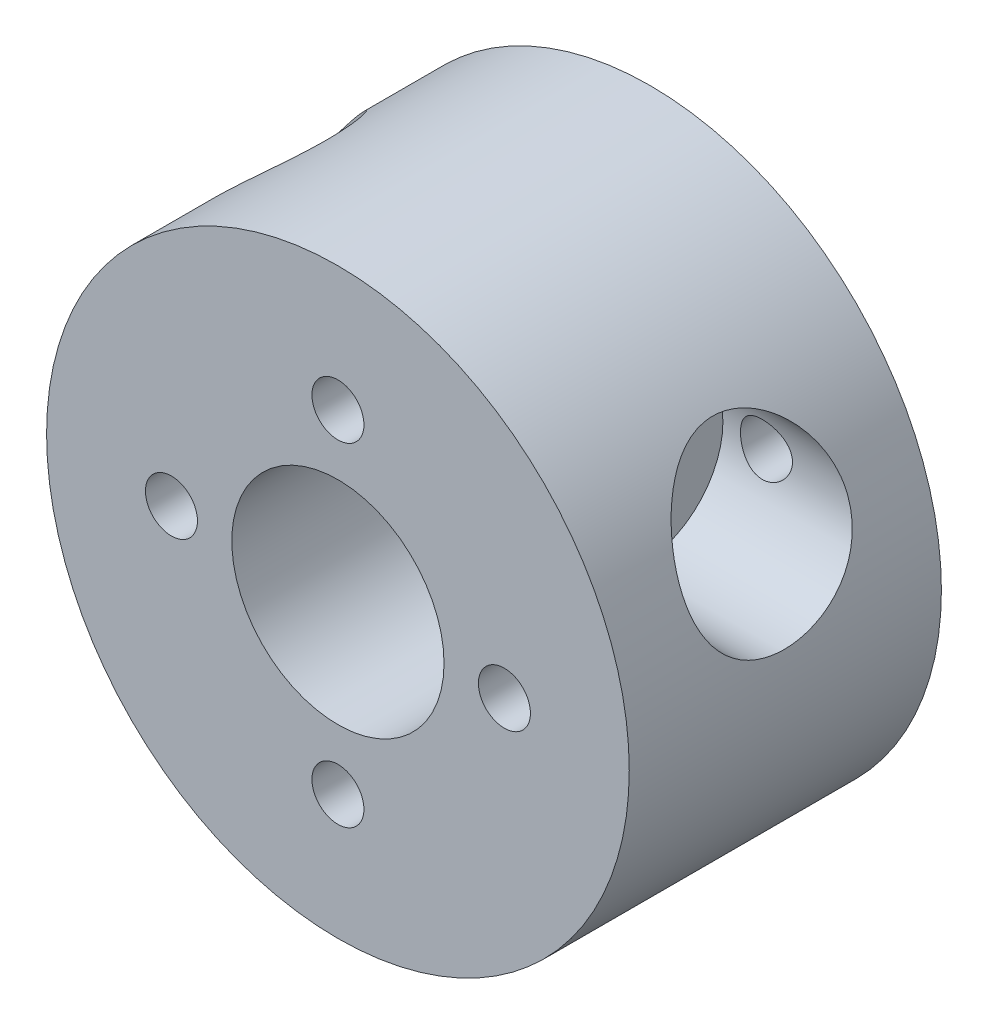
SolidWorks part; units mm, degrees
material "1060 Alloy"
ref_plane "Front Plane" through (0, 0, 0) normal (0, 0, 1) x (1, 0, 0)
ref_plane "Top Plane" through (0, 0, 0) normal (0, 1, 0) x (1, 0, 0)
ref_plane "Right Plane" through (0, 0, 0) normal (1, 0, 0) x (0, 0, -1)
sketch "Sketch1" plane through (0, 0, 0) normal (0, 0, 1) x (1, 0, 0)
  circle A0 centre (0, 0) radius 14
  circle A1 centre (0, 0) radius 5.1
extrude "Boss-Extrude1" add sketch "Sketch1" along normal blind 15
sketch "Sketch7" plane through (0, 0, 15) normal (0, 0, 1) x (1, 0, 0)
  circle A1 centre (0, 0) radius 14
  circle A2 centre (0, 0) radius 8
  point P3 (0, -8)
  point P5 (-8, 0)
  point P6 (0, 8)
  point P7 (8, 0)
hole_wizard "M3 Tapped Hole1" positions "Sketch9" profile "Sketch11" tap size "M3" standard "ISO"
sketch "Sketch9" plane through (0, 0, 15) normal (0, 0, 1) x (1, 0, 0)
  point P0 (0, -8)
  point P3 (-8, 0)
  point P6 (0, 8)
  point P9 (8, 0)
sketch "Sketch11" plane through (0, -8, 15) normal (1, 0, 0) x (0, -1, 0)
  line L0 (0, 0) -> (0, 7.2511)
  line L1 (0, 7.2511) -> (1.25, 6.5)
  line L2 (1.25, 6.5) -> (1.25, 0)
  line L5 (1.25, 0) -> (0, 0)
  line L10 (0, 7.2511) -> (-1.25, 6.5) construction
  line L11 (0, -6.35) -> (0, 107.95) construction
  dimension "Tap Drill Dia." = 2.5
  dimension "Tap Drill Depth" = 6.5
  dimension "Drill Angle" = 118
cosmetic thread "Hole Thread12" parameters "D1"=5, "D2"=3
cosmetic thread "Hole Thread13" parameters "D1"=5, "D2"=3
cosmetic thread "Hole Thread14" parameters "D1"=5, "D2"=3
cosmetic thread "Hole Thread15" parameters "D1"=5, "D2"=3
sketch "Sketch12" plane through (0, 0, 0) normal (0, 0, -1) x (-1, 0, 0)
  circle A0 centre (0, 0) radius 10.5 construction
  point P3 (0, -10.5)
  point P6 (-9.0933, 5.25)
  point P7 (9.0933, 5.25)
  point P8 (0, 0)
  dimension "D1" = 3
hole_wizard "M3 Tapped Hole2" positions "Sketch13" profile "Sketch15" tap size "M3" standard "ISO"
sketch "Sketch13" plane through (0, 0, 0) normal (0, 0, -1) x (-1, 0, 0)
  point P0 (0, -10.5)
  point P3 (-9.0933, 5.25)
  point P6 (9.0933, 5.25)
sketch "Sketch15" plane through (0, -10.5, 0) normal (1, 0, 0) x (0, 1, 0)
  line L0 (0, 0) -> (0, 7.2511)
  line L1 (0, 7.2511) -> (1.25, 6.5)
  line L2 (1.25, 6.5) -> (1.25, 0)
  line L5 (1.25, 0) -> (0, 0)
  line L10 (0, 7.2511) -> (-1.25, 6.5) construction
  line L11 (0, -6.35) -> (0, 107.95) construction
  dimension "Tap Drill Dia." = 2.5
  dimension "Tap Drill Depth" = 6.5
  dimension "Drill Angle" = 118
cosmetic thread "Hole Thread16" parameters "D1"=5, "D2"=3
cosmetic thread "Hole Thread17" parameters "D1"=5, "D2"=3
cosmetic thread "Hole Thread18" parameters "D1"=5, "D2"=3
ref_plane "Plane1" through (14, 0, 0) normal (1, 0, 0) x (0, 0, -1)
sketch "Sketch19" plane through (14, 0, 0) normal (1, 0, 0) x (0, 0, -1)
  line L0 (-6.5, 5.25) -> (0, 5.25) construction
  line L1 (-6.5, 5.25) -> (-7.2511, 5.25) construction
  circle A0 centre (-7.5, 5.25) radius 4
extrude "Cut-Extrude3" cut sketch "Sketch19" against normal blind 7
pattern_circular "CirPattern2" count 3 over 360 about axis through (0, 0, 0) along (0, 0, 1) of "Cut-Extrude3"
